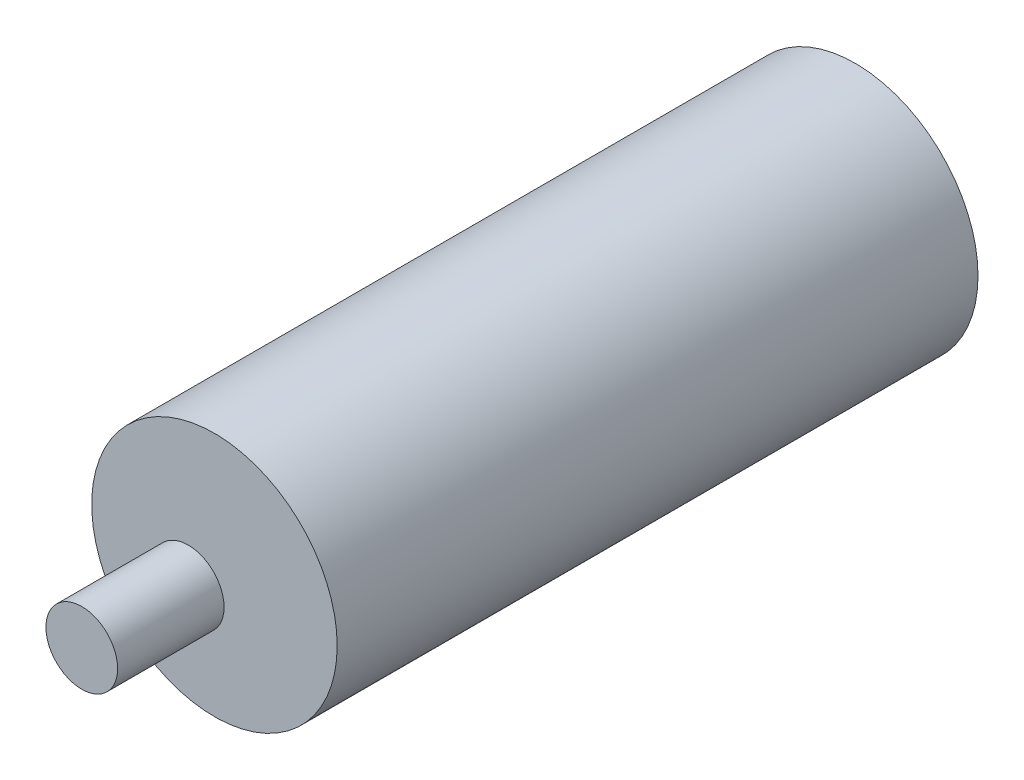
SolidWorks part; units mm, degrees
ref_plane "Front Plane" through (0, 0, 0) normal (0, 0, 1) x (1, 0, 0)
ref_plane "Top Plane" through (0, 0, 0) normal (0, 1, 0) x (1, 0, 0)
ref_plane "Right Plane" through (0, 0, 0) normal (1, 0, 0) x (0, 0, -1)
sketch "Sketch2" plane through (0, 0, 0) normal (0, 0, 1) x (1, 0, 0)
  circle A0 centre (0, 0) radius 28.702
  dimension "D1" = 57.404
extrude "Boss-Extrude1" add sketch "Sketch2" along normal blind 149.86
sketch "Sketch3" plane through (0, 0, 149.86) normal (0, 0, 1) x (1, 0, 0)
  circle A1 centre (-6.1321, -5.3855) radius 8.382
  dimension "D1" = 16.764
extrude "Boss-Extrude2" add sketch "Sketch3" along normal blind 24.892
